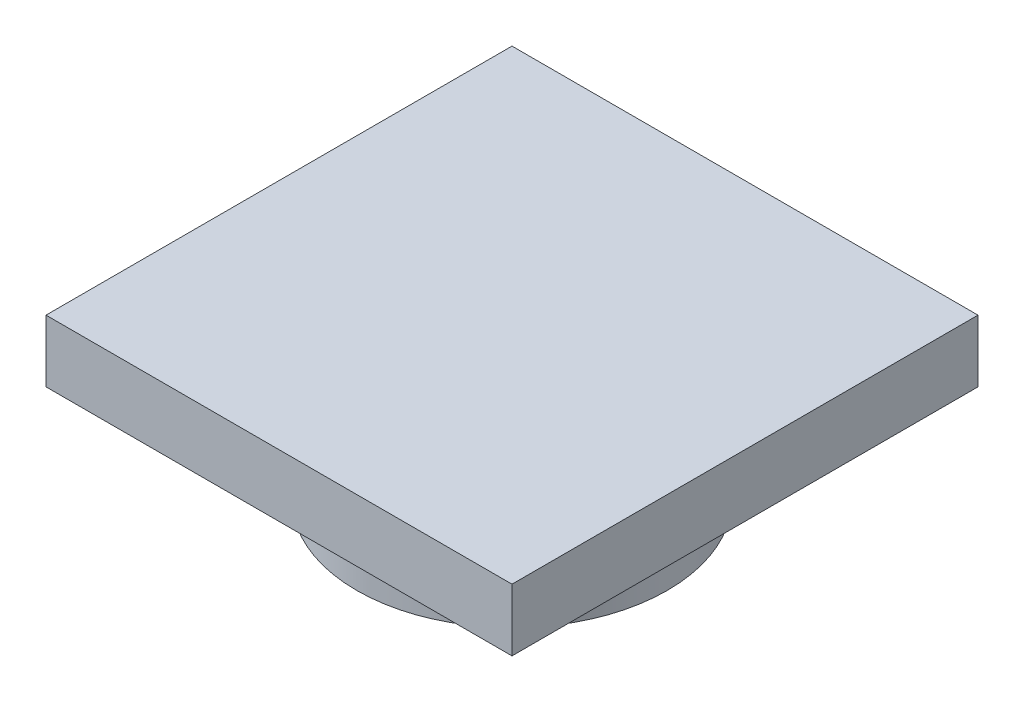
SolidWorks part; units mm, degrees
ref_plane "Front Plane" through (0, 0, 0) normal (0, 0, 1) x (1, 0, 0)
ref_plane "Top Plane" through (0, 0, 0) normal (0, 1, 0) x (1, 0, 0)
ref_plane "Right Plane" through (0, 0, 0) normal (1, 0, 0) x (0, 0, -1)
sketch "Sketch1" plane through (0, 0, 0) normal (0, 1, 0) x (1, 0, 0)
  circle A0 centre (0, 0) radius 5
  dimension "D1" = 10
extrude "Boss-Extrude1" add sketch "Sketch1" along normal blind 3.175
sketch "Sketch2" plane through (0, 0, 0) normal (0, -1, 0) x (1, 0, 0)
  circle A0 centre (0, 0) radius 1
  dimension "D1" = 2
extrude "Cut-Extrude1" cut sketch "Sketch2" against normal blind 3.175
sketch "Sketch3" plane through (0, 3.175, 0) normal (0, 1, 0) x (1, 0, 0)
  line L1 (-7.5, 7.5) -> (7.5, 7.5)
  line L2 (-7.5, 7.5) -> (-7.5, -7.5)
  line L3 (-7.5, -7.5) -> (7.5, -7.5)
  line L4 (7.5, 7.5) -> (7.5, -7.5)
  line L5 (-7.5, 7.5) -> (7.5, -7.5) construction
  line L6 (-7.5, -7.5) -> (7.5, 7.5) construction
  point P0 (0, 0)
  dimension "D1" = 15
  dimension "D2" = 15
extrude "Boss-Extrude2" add sketch "Sketch3" along normal blind 2
